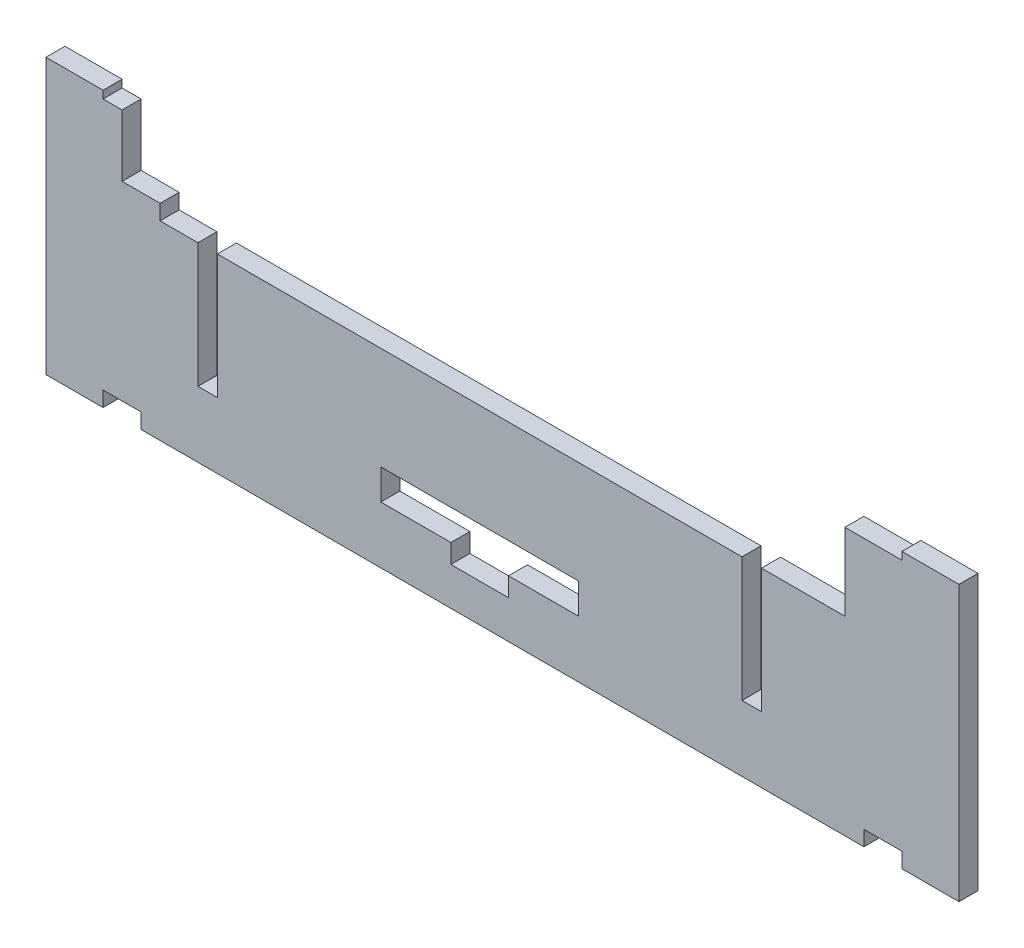
SolidWorks part; units mm, degrees
material "Acrylic (Medium-high impact)"
ref_plane "Front Plane" through (0, 0, 0) normal (0, 0, 1) x (1, 0, 0)
ref_plane "Top Plane" through (0, 0, 0) normal (0, 1, 0) x (1, 0, 0)
ref_plane "Right Plane" through (0, 0, 0) normal (1, 0, 0) x (0, 0, -1)
sketch "Sketch1" plane through (0, 0, 0) normal (0, 0, 1) x (1, 0, 0)
  line L0 (0, 0) -> (240, 0)
  line L2 (210, 54) -> (210, 50)
  line L3 (240, 0) -> (240, 72.25)
  line L4 (30, 50) -> (30, 54)
  line L5 (30, 54) -> (20, 54)
  line L6 (240, 72.25) -> (225, 72.25)
  line L7 (225, 72.25) -> (225, 70.25)
  line L8 (225, 70.25) -> (210, 70.25)
  line L9 (210, 70.25) -> (210, 54)
  line L10 (210, 50) -> (30, 50)
  line L11 (20, 54) -> (20, 70.25)
  line L12 (20, 70.25) -> (15, 70.25)
  line L13 (15, 70.25) -> (15, 72.25)
  line L14 (15, 72.25) -> (0, 72.25)
  line L17 (0, 72.25) -> (0, 0)
  dimension "D1" = 20
  dimension "D2" = 30
  dimension "D3" = 240
  dimension "D4" = 15
  dimension "D5" = 2
  dimension "D6" = 22.25
  dimension "D7" = 50
  dimension "D8" = 10
  dimension "D9" = 4
extrude "Boss-Extrude1" add sketch "Sketch1" along normal blind 5
ref_plane "Plane1" through (0, 50, 0) normal (0, 1, 0) x (-1, 0, 0)
extrude "Cut-Extrude6" cut sketch "Sketch7" along normal blind 32.7
sketch "Sketch7" plane through (76.9623, 50, 79.9822) normal (0, -1, 0) x (0.2993, 0, -0.9541)
  line L0 (89.5657, 88.3679) -> (121.0158, 78.5012)
  line L1 (89.5657, 88.3679) -> (88.0316, 83.4779)
  line L2 (121.0158, 78.5012) -> (119.4817, 73.6112)
  line L3 (88.0316, 83.4779) -> (119.4817, 73.6112)
  line L4 (88.7986, 85.9229) -> (120.2488, 76.0562) construction
  line L5 (120.3477, 133.1166) -> (125.1184, 131.6199) construction
  line L6 (48.5061, -95.8785) -> (120.3477, 133.1166) construction
  dimension "D1" = 54.4736
  dimension "D2" = 5.125
extrude "Cut-Extrude7" cut sketch "Sketch8" along normal blind 32.7
sketch "Sketch8" plane through (151.0641, 50, -36.8163) normal (0, -1, 0) x (-0.2993, 0, 0.9541)
  line L0 (48.2699, 101.3235) -> (121.0158, 78.5012)
  line L1 (48.2699, 101.3235) -> (46.7358, 96.4335)
  line L2 (121.0158, 78.5012) -> (119.4817, 73.6112)
  line L3 (46.7358, 96.4335) -> (119.4817, 73.6112)
  line L4 (85.1184, 131.6199) -> (13.2768, -97.3752) construction
  line L5 (120.2488, 76.0562) -> (47.5028, 98.8785) construction
  line L6 (85.1184, 131.6199) -> (80.3477, 133.1166) construction
  dimension "D1" = 42.5
  dimension "D2" = 5.125
extrude "Cut-Extrude8" cut sketch "Sketch9" against normal blind 50
sketch "Sketch9" plane through (179.8229, 98.1669, 0) normal (0, 0, -1) x (-1, 0, 0)
  line L0 (91.8097, -83.1669) -> (73.3847, -83.1669)
  line L1 (39.8097, -83.1669) -> (39.8097, -75.1669)
  line L2 (39.8097, -75.1669) -> (91.8097, -75.1669)
  line L3 (91.8097, -75.1669) -> (91.8097, -83.1669)
  line L4 (58.2347, -88.1669) -> (58.2347, -83.1669)
  line L5 (65.8097, -75.1669) -> (65.8097, -88.1669) construction
  line L7 (-60.1771, -98.1669) -> (-60.1771, -25.9169) construction
  line L9 (73.3847, -83.1669) -> (73.3847, -88.1669)
  line L10 (58.2347, -88.1669) -> (73.3847, -88.1669)
  line L12 (179.8229, -98.1669) -> (-60.1771, -98.1669) construction
  line L13 (58.2347, -83.1669) -> (39.8097, -83.1669)
  dimension "D1" = 8
  dimension "D2" = 125.9868
  dimension "D4" = 10
  dimension "D5" = 15.15
  dimension "D6" = 5
  dimension "D7" = 52
sketch "Sketch10" plane through (0, 0, 5) normal (0, 0, 1) x (1, 0, 0)
  line L0 (15, 0) -> (15, 4)
  line L1 (15, 0) -> (25, 0)
  line L2 (15, 4) -> (25, 4)
  line L3 (25, 0) -> (25, 4)
  line L4 (0, 0) -> (240, 0) construction
  line L5 (120, 0) -> (120, 50) construction
  line L6 (182.9639, 50) -> (45.0625, 50) construction
  line L7 (0, 72.25) -> (0, 0) construction
  line L8 (215, 0) -> (215, 4)
  line L9 (225, 4) -> (215, 4)
  line L10 (225, 0) -> (215, 0)
  line L11 (225, 0) -> (225, 4)
  dimension "D1" = 10
  dimension "D2" = 4
  dimension "D3" = 15
extrude "Cut-Extrude9" cut sketch "Sketch10" against normal through all
